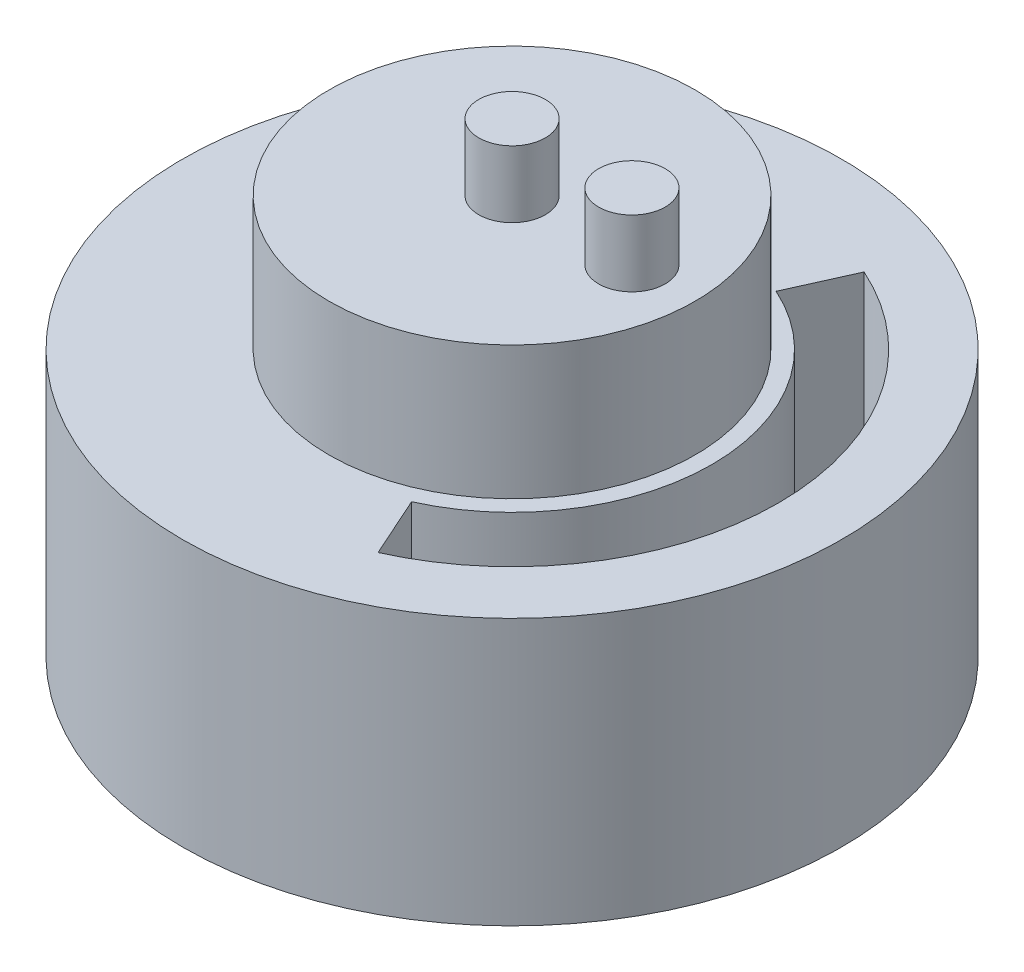
SolidWorks part; units mm, degrees
ref_plane "Plano frontal" through (0, 0, 0) normal (0, 0, 1) x (1, 0, 0)
ref_plane "Plano superior" through (0, 0, 0) normal (0, 1, 0) x (1, 0, 0)
ref_plane "Plano direito" through (0, 0, 0) normal (1, 0, 0) x (0, 0, -1)
sketch "Esboço1" plane through (0, 0, 0) normal (0, 1, 0) x (1, 0, 0)
  line L0 (0, 0) -> (-10, 0) construction
  line L1 (0, 0) -> (10, 0) construction
  line L2 (-10, 0) -> (-10, -17.3205) construction
  line L3 (10, 0) -> (10, -17.3205) construction
  line L4 (10, -27.2235) -> (-10, -27.2235) construction
  line L9 (-10, -22.9129) -> (-10, -27.2235) construction
  line L11 (10, -22.9129) -> (10, -27.2235) construction
  arc A1 (12.375, -21.4341) -> (-12.375, -21.4341) centre (0, 0) ccw
  circle A3 centre (0, 0) radius 24.75
extrude "Ressalto-extrusão2" add sketch "Esboço1" along normal blind 20
ref_plane "Plano1" through (0, 20, 0) normal (0, 1, 0) x (1, 0, 0)
sketch "Esboço3" plane through (0, 20, 0) normal (0, 1, 0) x (1, 0, 0)
  circle A0 centre (0, 0) radius 13.75
extrude "Boss-Extrude1" add sketch "Esboço3" along normal blind 10
sketch "Sketch1" plane through (0, 20, 0) normal (0, 1, 0) x (1, 0, 0)
  circle A0 centre (0, 0) radius 20
  circle A1 centre (0, 0) radius 25
ref_plane "Plane1" through (0, 30, 0) normal (0, 1, 0) x (1, 0, 0)
sketch "Sketch2" plane through (0, 30, 0) normal (0, 1, 0) x (1, 0, 0)
  line L0 (0, 0) -> (9, 0) construction
  circle A0 centre (0, 0) radius 2.5
  circle A1 centre (9, 0) radius 2.5
extrude "Boss-Extrude2" add sketch "Sketch2" along normal blind 5
ref_plane "Plane2" through (0, 20, 0) normal (0, 1, 0) x (1, 0, 0)
sketch "Sketch3" plane through (0, 20, 0) normal (0, 1, 0) x (1, 0, 0)
  line L0 (0, 0) -> (15, 0) construction
  line L1 (0, 0) -> (8.1857, -18.2481) construction
  line L2 (0, 0) -> (8.1857, 18.2481) construction
  line L3 (8.1857, -18.2481) -> (6.1393, -13.6861)
  line L4 (8.1857, 18.2481) -> (6.1393, 13.6861)
  arc A0 (6.1393, -13.6861) -> (6.1393, 13.6861) centre (0, 0) ccw
  arc A1 (8.1857, -18.2481) -> (8.1857, 18.2481) centre (0, 0) ccw
  dimension "D1" = 65.84
extrude "Cut-Extrude2" cut sketch "Sketch3" against normal up to surface (20 mm away) up to face at (0, 0, 24.75)
